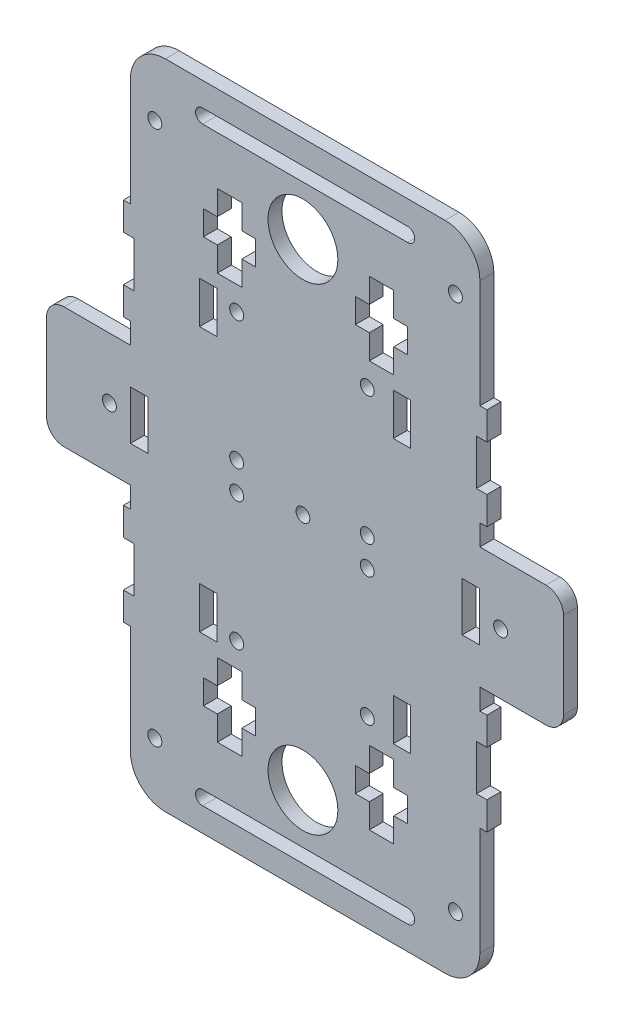
SolidWorks part; units mm, degrees
ref_plane "Front Plane" through (0, 0, 0) normal (0, 0, 1) x (1, 0, 0)
ref_plane "Top Plane" through (0, 0, 0) normal (0, 1, 0) x (1, 0, 0)
ref_plane "Right Plane" through (0, 0, 0) normal (1, 0, 0) x (0, 0, -1)
sketch "Sketch1" plane through (0, 0, 0) normal (0, 0, 1) x (1, 0, 0)
  line L0 (75, 4.4244) -> (-75, 4.4244) construction
  line L1 (0, 72.7324) -> (0, -63.8836) construction
  line L2 (-49.4, 97.7754) -> (-49.4, 48.7754)
  line L3 (-49.4, 21.7754) -> (-73.4, 21.7754)
  line L4 (-73.4, 21.7754) -> (-73.4, -12.9246)
  line L5 (-73.4, -12.9246) -> (-49.4, -12.9246)
  line L6 (-49.4, -12.9246) -> (-49.4, -26.9246)
  line L7 (50.6691, 97.7754) -> (-49.4, 97.7754) construction
  line L8 (50.6, -12.9246) -> (50.6, -26.9246)
  line L9 (50.6, -12.9246) -> (74.6, -12.9246)
  line L10 (74.6, -12.9246) -> (74.6, 21.7754)
  line L11 (74.6, 21.7754) -> (50.6691, 21.7754)
  line L12 (50.6691, 97.7754) -> (50.6691, 48.7754)
  line L13 (0, 72.7324) -> (0, 138.6441) construction
  line L14 (-73.4946, 97.7754) -> (-49.4, 97.7754)
  line L15 (50.6691, 97.7754) -> (74.6691, 97.7754)
  line L16 (-73.3495, -88.9246) -> (-49.4, -88.9246)
  line L17 (50.6, -88.9246) -> (74.5495, -88.9246)
  line L18 (-49.4, 48.7754) -> (-48.4, 48.7754)
  line L19 (-48.4, 48.7754) -> (-48.4, 35.7754)
  line L20 (-48.4, 35.7754) -> (-49.4, 35.7754)
  line L21 (-49.4, 35.7754) -> (-49.4, 21.7754)
  line L22 (50.6691, 48.7754) -> (49.6691, 48.7754)
  line L23 (49.6691, 48.7754) -> (49.6691, 35.7754)
  line L24 (49.6691, 35.7754) -> (50.6691, 35.7754)
  line L25 (50.6691, 35.7754) -> (50.6691, 21.7754)
  line L26 (-49.4, -26.9246) -> (-48.4, -26.9246)
  line L27 (-48.4, -39.9246) -> (-49.4, -39.9246)
  line L28 (-49.4, -39.9246) -> (-49.4, -88.9246)
  line L29 (-48.4, -26.9246) -> (-48.4, -39.9246)
  line L30 (-49.4, -88.9246) -> (50.6, -88.9246) construction
  line L31 (50.6, -26.9246) -> (49.6, -26.9246)
  line L32 (49.6, -26.9246) -> (49.6, -39.9246)
  line L33 (49.6, -39.9246) -> (50.6, -39.9246)
  line L34 (50.6, -39.9246) -> (50.6, -88.9246)
  line L36 (-48.4, 33.9331) -> (-48.4, 66.1831) construction
  circle A2 centre (0, 72.7324) radius 10
  circle A3 centre (0, -63.8836) radius 10
  circle A4 centre (0, 4.4244) radius 1.9726
  ellipse E0 centre (0.5873, 97.7754) end of major axis (-73.4946, 97.7754) minor radius 35 (-73.4946, 97.7754) -> (74.6691, 97.7754) cw
  ellipse E1 centre (0.6, -88.9246) end of major axis (74.6, -90.6246) minor radius 34.5333 (-73.3495, -88.9246) -> (74.5495, -88.9246) ccw
  point P4 (0, 4.4244)
  point P8 (0, 4.4244)
  point P39 (-0.1931, -123.4488)
  point P53 (-49.4, 97.7754)
  dimension "D11" = 13
  dimension "D12" = 49
  dimension "D13" = 34.7
  dimension "D1" = 49
  dimension "D9" = 49
  dimension "D10" = 14
  dimension "D2" = 13
  dimension "D3" = 14
  dimension "D4" = 14
  dimension "D5" = 13
  dimension "D6" = 49
  dimension "D7" = 14
  dimension "D8" = 13
  dimension "D14" = 34.7
  dimension "D15" = 1
  dimension "D16" = 1
  dimension "D17" = 1
  dimension "D18" = 1
  dimension "D19" = 1
  dimension "D20" = 1
  dimension "D21" = 1
  dimension "D22" = 1
  dimension "D23" = 23.9495
  dimension "D24" = 23.9495
  dimension "D25" = 24
  dimension "D26" = 24.0946
  dimension "D27" = 24
  dimension "D28" = 23.9309
  dimension "D29" = 24
  dimension "D30" = 24
extrude "Boss-Extrude2" add sketch "Sketch1" along normal blind 4
sketch "Sketch5" plane through (0, 0, 0) normal (0, 0, -1) x (-1, 0, 0)
  line L0 (49.4, 21.7754) -> (73.4, 21.7754) construction
  line L1 (44.4, 11.4254) -> (49.4, 11.4254)
  line L2 (44.4, 11.4254) -> (44.4, -2.5746)
  line L3 (44.4, -2.5746) -> (49.4, -2.5746)
  line L4 (49.4, 11.4254) -> (49.4, -2.5746)
  line L5 (73.4, 21.7754) -> (73.4, -12.9246) construction
  dimension "D1" = 5
  dimension "D2" = 14
  dimension "D3" = 10.35
  dimension "D4" = 10.35
  dimension "D5" = 29
extrude "Cut-Extrude3" cut sketch "Sketch5" against normal through all
sketch "Sketch6" plane through (0, 0, 0) normal (0, 0, -1) x (-1, 0, 0)
  line L0 (-74.6, -12.9246) -> (-74.6, 21.7754) construction
  line L1 (-50.6, 11.4254) -> (-45.6, 11.4254)
  line L2 (-50.6, 11.4254) -> (-50.6, -2.5746)
  line L3 (-50.6, -2.5746) -> (-45.6, -2.5746)
  line L4 (-45.6, 11.4254) -> (-45.6, -2.5746)
  line L5 (-50.6, -12.9246) -> (-74.6, -12.9246) construction
  line L6 (-74.6, 21.7754) -> (-50.6691, 21.7754) construction
  dimension "D1" = 5
  dimension "D2" = 14
  dimension "D3" = 29
  dimension "D4" = 10.35
  dimension "D5" = 10.35
extrude "Cut-Extrude4" cut sketch "Sketch6" against normal through all
sketch "Sketch19" plane through (0, 0, 0) normal (0, 0, -1) x (-1, 0, 0)
  line L1 (-50.6, 11.4254) -> (-50.6, -2.5746) construction
  circle A0 centre (-56.6, 4.4254) radius 2
  point P3 (-56.6, 4.4254)
  point P4 (-50.6, 4.4254)
extrude "Cut-Extrude19" cut sketch "Sketch19" against normal through all
sketch "Sketch22" plane through (0, 0, 0) normal (0, 0, -1) x (-1, 0, 0)
  line L1 (49.4, 97.7754) -> (49.4, 48.7754) construction
  line L2 (-50.6691, 48.7754) -> (-50.6691, 97.7754) construction
  circle A0 centre (42.4, 81) radius 2
  circle A1 centre (-43.6691, 81) radius 2
  point P5 (4, 81)
  dimension "D1" = 4
  dimension "D3" = 4
  dimension "D2" = 7
  dimension "D4" = 7
extrude "Cut-Extrude22" cut sketch "Sketch22" against normal through all
sketch "Sketch23" plane through (0, 0, 4) normal (0, 0, 1) x (1, 0, 0)
  line L0 (-49.4, -39.9246) -> (-49.4, -88.9246) construction
  line L2 (50.6, -88.9246) -> (50.6, -39.9246) construction
  circle A0 centre (43.6, -81) radius 2
  circle A1 centre (-42.4, -81) radius 2
  point P4 (0.6147, -81)
  point P10 (0.6147, -81)
  dimension "D1" = 4
  dimension "D3" = 4
  dimension "D2" = 7
  dimension "D4" = 7
extrude "Cut-Extrude23" cut sketch "Sketch23" against normal through all
sketch "Sketch24" plane through (0, 0, 4) normal (0, 0, 1) x (1, 0, 0)
  line L0 (50.6691, 97.7754) -> (74.6691, 97.7754) construction
  line L1 (-73.4946, 97.7754) -> (-49.4, 97.7754) construction
  line L2 (74.5495, -88.9246) -> (50.6, -88.9246) construction
  line L3 (-49.4, -88.9246) -> (-73.3495, -88.9246) construction
  circle A0 centre (-50, -94.9246) radius 2
  circle A1 centre (50, -94.9246) radius 2
  circle A2 centre (-50, 103.7754) radius 2
  circle A3 centre (50, 103.7754) radius 2
  dimension "D1" = 4
  dimension "D3" = 4
  dimension "D9" = 4
  dimension "D10" = 4
  dimension "D11" = 6
  dimension "D12" = 6
  dimension "D13" = 6
  dimension "D14" = 6
extrude "Cut-Extrude24" cut sketch "Sketch24" against normal through all
sketch "Sketch25" plane through (0, 0, 0) normal (0, 0, -1) x (-1, 0, 0)
  line L1 (-30.8691, 48.2754) -> (-30.8691, 34.1932) construction
  line L5 (-30.8691, 48.2754) -> (-25.8691, 48.2754)
  line L6 (-30.8691, 48.2754) -> (-30.8691, 36.2754)
  line L7 (-30.8691, 36.2754) -> (-25.8691, 36.2754)
  line L8 (-25.8691, 48.2754) -> (-25.8691, 36.2754)
  line L12 (24.6, 48.2754) -> (29.6, 48.2754)
  line L13 (24.6, 48.2754) -> (24.6, 36.2754)
  line L14 (24.6, 36.2754) -> (29.6, 36.2754)
  line L15 (29.6, 48.2754) -> (29.6, 36.2754)
  line L22 (-30.8, -27.4246) -> (-25.8, -27.4246)
  line L23 (-30.8, -27.4246) -> (-30.8, -39.4246)
  line L24 (-30.8, -39.4246) -> (-25.8, -39.4246)
  line L25 (-25.8, -27.4246) -> (-25.8, -39.4246)
  line L26 (24.6, -27.4246) -> (29.6, -27.4246)
  line L27 (24.6, -27.4246) -> (24.6, -39.4246)
  line L28 (24.6, -39.4246) -> (29.6, -39.4246)
  line L29 (29.6, -27.4246) -> (29.6, -39.4246)
  dimension "D1" = 12
  dimension "D2" = 5
  dimension "D3" = 12
  dimension "D4" = 12
  dimension "D5" = 5
  dimension "D6" = 12
  dimension "D7" = 5
  dimension "D8" = 5
extrude "Cut-Extrude25" cut sketch "Sketch25" against normal through all
sketch "Sketch29" plane through (0, 0, 0) normal (0, 0, -1) x (-1, 0, 0)
  line L4 (-30.291, -39.4246) -> (-30.291, -50.2246) construction
  line L5 (-30.8, -39.4246) -> (-25.8, -39.4246) construction
  line L6 (29.1154, -39.4246) -> (29.1154, -50.2246) construction
  line L7 (24.6, -39.4246) -> (29.6, -39.4246) construction
sketch "Sketch26" plane through (0, 0, 0) normal (0, 0, -1) x (-1, 0, 0)
  line L0 (24.5102, 52.0754) -> (17.5102, 52.0754)
  line L1 (24.5102, 52.0754) -> (24.5102, 59.0754) construction
  line L2 (-25.9991, 73.0754) -> (-18.9991, 73.0754) construction
  line L3 (17.5102, 52.0754) -> (17.5102, 59.0754)
  line L4 (17.5102, 59.0754) -> (13.5102, 59.0754)
  line L5 (-29.9991, 59.0754) -> (-29.9991, 66.0754)
  line L6 (13.5102, 59.0754) -> (13.5102, 66.0754)
  line L7 (-14.9991, 66.0754) -> (-14.9991, 59.0754)
  line L8 (13.5102, 66.0754) -> (17.5102, 66.0754)
  line L9 (-25.9991, 52.0754) -> (-18.9991, 52.0754)
  line L10 (-18.9991, 52.0754) -> (-18.9991, 59.0754)
  line L11 (-18.9991, 59.0754) -> (-14.9991, 59.0754)
  line L12 (-14.9991, 66.0754) -> (-18.9991, 66.0754)
  line L13 (-18.9991, 66.0754) -> (-18.9991, 73.0754)
  line L14 (-18.9991, 73.0754) -> (-25.9991, 73.0754)
  line L15 (-25.9991, 73.0754) -> (-25.9991, 66.0754)
  line L16 (-25.9991, 66.0754) -> (-29.9991, 66.0754)
  line L17 (-29.9991, 59.0754) -> (-25.9991, 59.0754)
  line L18 (-25.9991, 59.0754) -> (-25.9991, 52.0754)
  line L19 (17.5102, 66.0754) -> (17.5102, 73.0754)
  line L20 (17.5102, 73.0754) -> (24.5102, 73.0754)
  line L21 (24.5102, 73.0754) -> (24.5102, 66.0754)
  line L22 (24.5102, 66.0754) -> (28.5102, 66.0754)
  line L23 (28.5102, 66.0754) -> (28.5102, 59.0754)
  line L24 (28.5102, 59.0754) -> (24.5102, 59.0754)
  line L27 (29.1154, -39.4246) -> (29.1154, -50.2246) construction
  line L28 (-30.291, -39.4246) -> (-30.291, -50.2246) construction
  line L35 (24.5102, 59.0754) -> (24.5102, 52.0754)
  line L36 (-19, -69) -> (-19, -62)
  line L37 (-26, -48) -> (-19, -48)
  line L38 (-19, -48) -> (-19, -55)
  line L39 (-19, -55) -> (-15, -55)
  line L40 (-15, -55) -> (-15, -62)
  line L41 (-15, -62) -> (-19, -62)
  line L42 (-19, -69) -> (-26, -69)
  line L43 (-26, -69) -> (-26, -62)
  line L44 (-26, -62) -> (-30, -62)
  line L45 (-30, -62) -> (-30, -55)
  line L46 (-30, -55) -> (-26, -55)
  line L47 (-26, -55) -> (-26, -48)
  line L49 (24.5102, -48) -> (17.5102, -48)
  line L50 (17.5102, -48) -> (17.5102, -55)
  line L51 (17.5102, -55) -> (13.5102, -55)
  line L52 (13.5102, -55) -> (13.5102, -62)
  line L53 (13.5102, -62) -> (17.5102, -62)
  line L54 (17.5102, -62) -> (17.5102, -69)
  line L55 (17.5102, -69) -> (24.5102, -69)
  line L56 (24.5102, -69) -> (24.5102, -62)
  line L57 (24.5102, -62) -> (28.5102, -62)
  line L58 (28.5102, -62) -> (28.5102, -55)
  line L59 (28.5102, -55) -> (24.5102, -55)
  line L60 (24.5102, -55) -> (24.5102, -48)
  point P26 (-26, -48)
  dimension "D1" = 15
  dimension "D2" = 21
  dimension "D3" = 7
  dimension "D4" = 7
  dimension "D5" = 4
  dimension "D6" = 7
  dimension "D7" = 7
  dimension "D8" = 7
  dimension "D9" = 15
  dimension "D10" = 21
  dimension "D11" = 7
  dimension "D12" = 7
  dimension "D13" = 4
  dimension "D14" = 4
  dimension "D15" = 4
  dimension "D16" = 4
  dimension "D17" = 7
  dimension "D18" = 7
extrude "Cut-Extrude26" cut sketch "Sketch26" against normal through all
sketch "Sketch28" plane through (0, 0, 0) normal (0, 0, -1) x (-1, 0, 0)
  line L0 (-50.6691, 97.7754) -> (49.4, 97.7754) construction
  line L1 (30, -112) -> (-30, -112)
  line L2 (-30, 118.8223) -> (30, 118.8223) construction
  line L3 (-30, 120.8223) -> (30, 120.8223)
  line L4 (-30, 116.8223) -> (30, 116.8223)
  line L5 (-30, -112) -> (30, -112) construction
  line L6 (-30, -110) -> (30, -110)
  line L7 (-30, -114) -> (30, -114)
  line L8 (-65.7732, 104.3331) -> (-40.7732, 117.3331) construction
  line L9 (-66.6959, 106.1075) -> (-41.6959, 119.1075)
  line L10 (-64.8505, 102.5586) -> (-39.8505, 115.5586)
  line L11 (38.5049, 117.1628) -> (65.4902, 104.1735) construction
  line L12 (39.3724, 118.9649) -> (66.3577, 105.9756)
  line L13 (37.6375, 115.3607) -> (64.6228, 102.3714)
  line L14 (-50.6691, 88.9285) -> (49.4, 88.9285) construction
  line L15 (-50.6691, 48.7754) -> (-50.6691, 97.7754) construction
  line L16 (49.4, 97.7754) -> (49.4, 48.7754) construction
  line L17 (28.7309, 88.9285) -> (-30, 88.9285) construction
  line L18 (28.7309, 86.9285) -> (-30, 86.9285)
  line L19 (28.7309, 90.9285) -> (-30, 90.9285)
  line L21 (36, -112) -> (63, -99) construction
  line L22 (35.1324, -110.198) -> (62.1324, -97.198)
  line L23 (36.8676, -113.802) -> (63.8676, -100.802)
  line L24 (-63, -99) -> (-38, -112.1208) construction
  line L25 (-62.0706, -97.2291) -> (-37.0706, -110.3499)
  line L26 (-63.9294, -100.7709) -> (-38.9294, -113.8918)
  arc A0 (-30, 120.8223) -> (-30, 116.8223) centre (-30, 118.8223) ccw
  arc A1 (30, 116.8223) -> (30, 120.8223) centre (30, 118.8223) ccw
  arc A2 (-66.6959, 106.1075) -> (-64.8505, 102.5586) centre (-65.7732, 104.3331) ccw
  arc A3 (28.7309, 86.9285) -> (28.7309, 90.9285) centre (28.7309, 88.9285) ccw
  arc A4 (-39.8505, 115.5586) -> (-41.6959, 119.1075) centre (-40.7732, 117.3331) ccw
  arc A5 (39.3724, 118.9649) -> (37.6375, 115.3607) centre (38.5049, 117.1628) ccw
  arc A6 (64.6228, 102.3714) -> (66.3577, 105.9756) centre (65.4902, 104.1735) ccw
  arc A7 (35.1324, -110.198) -> (36.8676, -113.802) centre (36, -112) ccw
  arc A8 (-30, -110) -> (-30, -114) centre (-30, -112) ccw
  arc A9 (30, -114) -> (30, -110) centre (30, -112) ccw
  arc A10 (-30, 90.9285) -> (-30, 86.9285) centre (-30, 88.9285) ccw
  arc A11 (63.8676, -100.802) -> (62.1324, -97.198) centre (63, -99) ccw
  arc A12 (-62.0706, -97.2291) -> (-63.9294, -100.7709) centre (-63, -99) ccw
  arc A13 (-38.9294, -113.8918) -> (-37.0706, -110.3499) centre (-38, -112.1208) ccw
  point P4 (0, -112)
  point P6 (0, -112)
  point P10 (0, 118.8223)
  point P15 (-36, -112)
  point P16 (0, -112)
  point P22 (-30, -112)
  point P23 (-38, -112.1208)
  point P25 (65.4902, 104.1735)
  point P26 (-40.7732, 117.3331)
  point P29 (-53.2732, 110.8331)
  point P35 (34, -112)
  point P36 (38.5049, 117.1628)
  point P39 (51.9976, 110.6681)
  point P44 (30, -112)
  point P49 (-0.6346, 88.9285)
  point P57 (36, -112)
  point P60 (49.5, -105.5)
  point P65 (-50.5, -105.5604)
  dimension "D1" = 4
extrude "Cut-Extrude29" cut sketch "Sketch28" against normal through all contours L18 A10 L19 A3
sketch "Sketch20" plane through (0, 0, 0) normal (0, 0, -1) x (-1, 0, 0)
  circle A1 centre (55.4, 4.4254) radius 2
  dimension "D1" = 4
extrude "Cut-Extrude20" cut sketch "Sketch20" against normal through all
sketch "Sketch30" plane through (0, 0, 0) normal (0, 0, -1) x (-1, 0, 0)
  line L3 (-93.3825, 4.4254) -> (88.3139, 4.4254)
  line L4 (-93.3825, 4.4254) -> (-93.3825, -127.0315)
  line L5 (-93.3825, -127.0315) -> (88.3139, -127.0315)
  line L6 (88.3139, 4.4254) -> (88.3139, -127.0315)
extrude "Cut-Extrude30" cut sketch "Sketch30" against normal blind 4 contours L4 L3 L6 L5
ref_plane "Plane1" through (0, 4.4254, 0) normal (0, -1, 0) x (-1, 0, 0)
sketch "Sketch31" plane through (0, 0, 0) normal (0, 0, -1) x (-1, 0, 0)
  line L0 (21.7811, 5.0804) -> (-21.4189, 5.0804) construction
  line L1 (21.7811, 5.0804) -> (21.7811, 48.2804) construction
  line L2 (21.7811, 48.2804) -> (-21.4189, 48.2804) construction
  line L3 (-21.4189, 5.0804) -> (-21.4189, 48.2804) construction
  circle A0 centre (-18.413, 45.2129) radius 2
  circle A1 centre (-18.4137, 8.4729) radius 2
  circle A2 centre (18.967, 45.2129) radius 2
  circle A3 centre (18.9663, 8.4729) radius 2
  point P2 (0.1811, 26.6804)
  dimension "D1" = 43.2
  dimension "D2" = 43.2
  dimension "D3" = 36.74
  dimension "D4" = 37.38
  dimension "D5" = 36.74
  dimension "D6" = 37.38
  dimension "D7" = 52.4122
  dimension "D8" = 52.4132
extrude "Cut-Extrude31" cut sketch "Sketch31" against normal blind 4
sketch "Sketch32" plane through (0, 0, 0) normal (0, 0, -1) x (-1, 0, 0)
  line L1 (79.0694, 97.7754) -> (-88.3924, 97.7754)
  line L2 (79.0694, 97.7754) -> (79.0694, 135.0434)
  line L3 (79.0694, 135.0434) -> (-88.3924, 135.0434)
  line L4 (-88.3924, 97.7754) -> (-88.3924, 135.0434)
extrude "Cut-Extrude32" cut sketch "Sketch32" against normal blind 4
fillet "Fillet1" radius 10 2 edges at (-49.4, 97.7754, 2) (50.6691, 97.7754, 2)
fillet "Fillet2" radius 5 2 edges at (-73.4, 21.7754, 2) (74.6, 21.7754, 2)
sketch "Sketch33" plane through (0, 0, 4) normal (0, 0, 1) x (1, 0, 0)
  line L1 (50.6691, 48.7754) -> (52.6691, 48.7754)
  line L2 (50.6691, 48.7754) -> (50.6691, 56.7754)
  line L3 (50.6691, 56.7754) -> (52.6691, 56.7754)
  line L4 (52.6691, 48.7754) -> (52.6691, 56.7754)
  line L5 (50.6691, 35.7754) -> (52.6691, 35.7754)
  line L6 (50.6691, 35.7754) -> (50.6691, 27.7754)
  line L7 (50.6691, 27.7754) -> (52.6691, 27.7754)
  line L8 (52.6691, 35.7754) -> (52.6691, 27.7754)
  line L9 (-49.4, 35.7754) -> (-51.4, 35.7754)
  line L10 (-49.4, 35.7754) -> (-49.4, 27.7754)
  line L11 (-49.4, 27.7754) -> (-51.4, 27.7754)
  line L12 (-51.4, 35.7754) -> (-51.4, 27.7754)
  line L13 (-49.4, 48.7754) -> (-51.4, 48.7754)
  line L14 (-49.4, 48.7754) -> (-49.4, 56.7754)
  line L15 (-49.4, 56.7754) -> (-51.4, 56.7754)
  line L16 (-51.4, 48.7754) -> (-51.4, 56.7754)
  dimension "D1" = 8
  dimension "D2" = 2
  dimension "D3" = 8
  dimension "D4" = 2
  dimension "D5" = 8
  dimension "D6" = 2
  dimension "D7" = 8
  dimension "D8" = 2
extrude "Boss-Extrude3" add sketch "Sketch33" against normal blind 4
mirror "Mirror1" about plane through (0, 4.4254, 0) normal (0, -1, 0) of bodies 145
